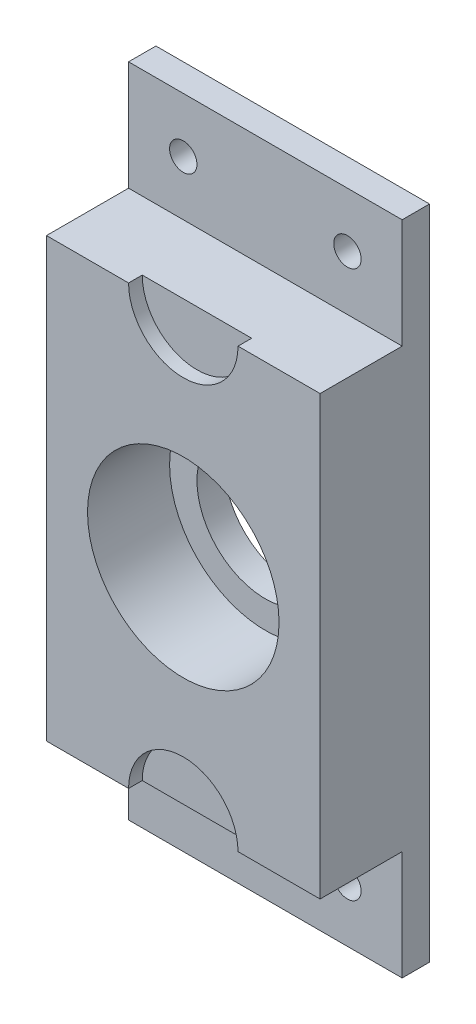
SolidWorks part; units mm, degrees
ref_plane "Front Plane" through (0, 0, 0) normal (0, 0, 1) x (1, 0, 0)
ref_plane "Top Plane" through (0, 0, 0) normal (0, 1, 0) x (1, 0, 0)
ref_plane "Right Plane" through (0, 0, 0) normal (1, 0, 0) x (0, 0, -1)
sketch "Sketch1" plane through (0, 0, 0) normal (0, 0, 1) x (1, 0, 0)
  line L1 (-31.75, -76.2) -> (31.75, -76.2)
  line L2 (-31.75, -76.2) -> (-31.75, 76.2)
  line L3 (-31.75, 76.2) -> (31.75, 76.2)
  line L4 (31.75, -76.2) -> (31.75, 76.2)
  line L5 (-31.75, -76.2) -> (31.75, 76.2) construction
  line L6 (-31.75, 76.2) -> (31.75, -76.2) construction
  line L7 (-31.75, -76.2) -> (-19.05, -76.2)
  line L8 (-31.75, -76.2) -> (-31.75, -63.5)
  line L9 (-31.75, -63.5) -> (-19.05, -63.5)
  line L10 (-19.05, -76.2) -> (-19.05, -63.5)
  line L11 (31.75, -76.2) -> (19.05, -76.2)
  line L12 (31.75, -76.2) -> (31.75, -63.5)
  line L13 (31.75, -63.5) -> (19.05, -63.5)
  line L14 (19.05, -76.2) -> (19.05, -63.5)
  line L15 (31.75, 76.2) -> (19.05, 76.2)
  line L16 (31.75, 76.2) -> (31.75, 63.5)
  line L17 (31.75, 63.5) -> (19.05, 63.5)
  line L18 (19.05, 76.2) -> (19.05, 63.5)
  line L19 (-31.75, 76.2) -> (-19.05, 76.2)
  line L20 (-31.75, 76.2) -> (-31.75, 63.5)
  line L21 (-31.75, 63.5) -> (-19.05, 63.5)
  line L22 (-19.05, 76.2) -> (-19.05, 63.5)
  circle A0 centre (-19.05, 63.5) radius 3.175
  circle A1 centre (19.05, 63.5) radius 3.175
  circle A2 centre (-19.05, -63.5) radius 3.175
  circle A3 centre (19.05, -63.5) radius 3.175
  point P0 (0, 0)
extrude "Boss-Extrude1" add sketch "Sketch1" along normal blind 25.4 contours A3 L13 L4 L17 A1 L18 L3 L22 A0 L21 L2 L9 A2 L10 L1 L14 | A0 L22 L3 L2 L21 | A1 L17 L4 L3 L18 | A2 L9 L2 L1 L10 | A3 L14 L1 L4 L13
sketch "Sketch2" plane through (0, 0, 25.4) normal (0, 0, 1) x (1, 0, 0)
  line L0 (31.75, -76.2) -> (31.75, 76.2) construction
  line L1 (-31.75, 76.2) -> (31.75, 76.2)
  line L2 (-31.75, 76.2) -> (-31.75, 50.8)
  line L3 (-31.75, 50.8) -> (31.75, 50.8)
  line L4 (31.75, 76.2) -> (31.75, 50.8)
  line L5 (-31.75, -76.2) -> (-31.75, 76.2) construction
  line L6 (31.75, -76.2) -> (-31.75, -76.2)
  line L7 (31.75, -76.2) -> (31.75, -50.8)
  line L8 (31.75, -50.8) -> (-31.75, -50.8)
  line L9 (-31.75, -76.2) -> (-31.75, -50.8)
extrude "Cut-Extrude1" cut sketch "Sketch2" against normal blind 19.05
sketch "Sketch3" plane through (0, 0, 25.4) normal (0, 0, 1) x (1, 0, 0)
  circle A0 centre (0, 0) radius 15.875
extrude "Cut-Extrude4" cut sketch "Sketch3" against normal through all
sketch "Sketch5" plane through (0, 0, 25.4) normal (0, 0, 1) x (1, 0, 0)
  circle A0 centre (0, 0) radius 15.875
  circle A1 centre (0, 0) radius 22.225
  dimension "D1" = 6.35
extrude "Cut-Extrude6" cut sketch "Sketch5" against normal blind 19.05
sketch "Sketch6" plane through (0, 0, 25.4) normal (0, 0, 1) x (1, 0, 0)
  line L0 (31.75, -50.8) -> (-31.75, -50.8) construction
  line L1 (-12.7, 0) -> (12.7, 0)
  circle A0 centre (0, -50.8) radius 12.7
  circle A1 centre (0, 50.8) radius 12.7
  point P9 (0, 0)
extrude "Cut-Extrude7" cut sketch "Sketch6" against normal blind 3.175 contours A1 | A0
sketch "Sketch7" plane through (-31.75, 0, 0) normal (-1, 0, 0) x (0, 0, 1)
  line L26 (6.35, -50.8) -> (25.4, -50.8) construction
  line L27 (0, 123.19) -> (19.05, 123.19)
  line L28 (6.35, -50.8) -> (19.05, -50.8)
  line L32 (25.4, 50.8) -> (6.35, 50.8)
  line L33 (6.35, 50.8) -> (6.35, 76.2)
  line L34 (6.35, 76.2) -> (0, 76.2)
  line L35 (0, 76.2) -> (0, -76.2)
  line L36 (0, -76.2) -> (6.35, -76.2)
  line L37 (6.35, -76.2) -> (6.35, -50.8)
  line L38 (6.35, -50.8) -> (25.4, -50.8)
  line L39 (25.4, -50.8) -> (25.4, 50.8)
  line L43 (0, 123.19) -> (0, -76.2)
  line L44 (0, -76.2) -> (6.35, -76.2)
  line L45 (6.35, -76.2) -> (6.35, -50.8)
  line L47 (19.05, -50.8) -> (19.05, 123.19)
  dimension "D2" = 19.05
  dimension "D3" = 173.99
  dimension "D1" = 0
extrude "Boss-Extrude2" add sketch "Sketch7" along normal blind 25.4 separate body
sketch "Sketch9" plane through (-57.15, 0, 0) normal (-1, 0, 0) x (0, 0, 1)
  line L0 (0, 123.19) -> (19.05, 123.19)
  line L1 (19.05, 123.19) -> (0, 123.19) construction
  line L2 (19.05, 123.19) -> (19.05, 119.634)
  line L3 (19.05, -50.8) -> (19.05, 123.19) construction
  line L4 (19.05, 119.634) -> (0, 119.634)
  line L5 (0, 123.19) -> (0, -76.2) construction
  line L6 (0, 119.634) -> (0, 123.19)
  line L7 (0, 112.014) -> (19.05, 112.014)
  line L8 (19.05, 112.014) -> (19.05, 108.458)
  line L9 (19.05, 108.458) -> (0, 108.458)
  line L10 (0, 108.458) -> (0, 112.014)
  dimension "D1" = 3.556
  dimension "D2" = 3.556
  dimension "D3" = 7.62
extrude "Boss-Extrude4" add sketch "Sketch9" along normal blind 35.56
delete or keep bodies "Body-Delete/Keep 1" type keep bodies bodies 108
